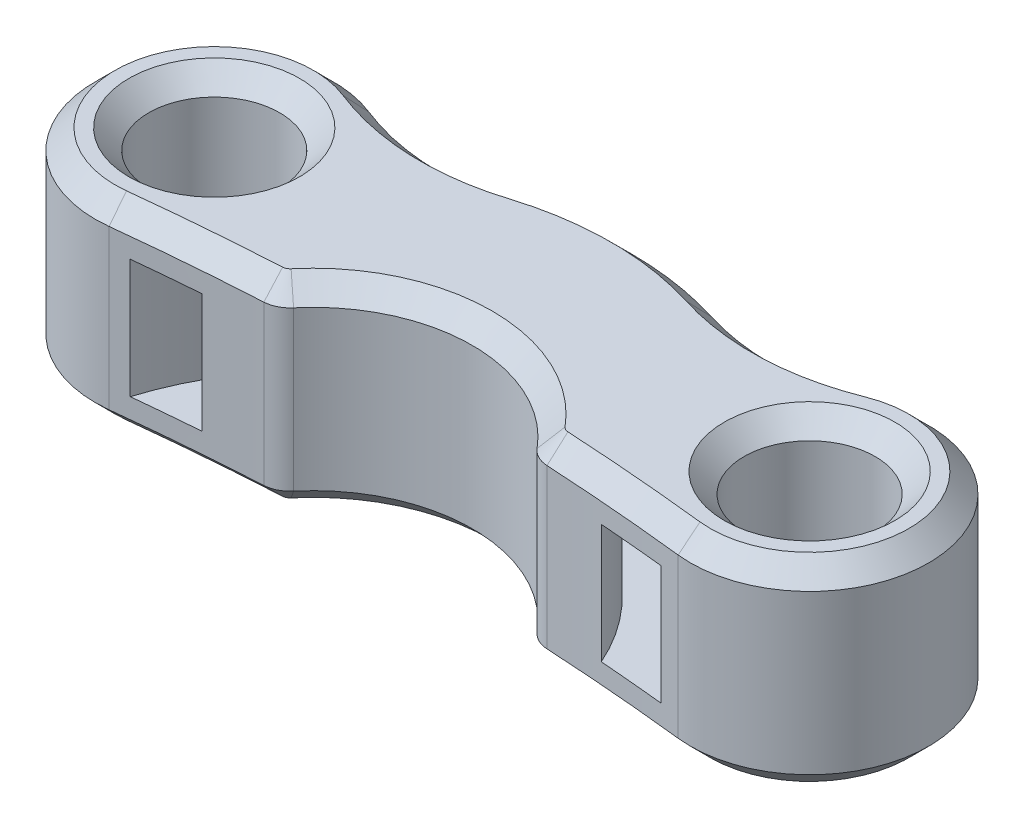
SolidWorks part; units mm, degrees
ref_plane "Front Plane" through (0, 0, 0) normal (0, 0, 1) x (1, 0, 0)
ref_plane "Top Plane" through (0, 0, 0) normal (0, 1, 0) x (1, 0, 0)
ref_plane "Right Plane" through (0, 0, 0) normal (1, 0, 0) x (0, 0, -1)
sketch "Sketch1" plane through (0, 0, 0) normal (0, 1, 0) x (1, 0, 0)
  line L0 (-7.5, 0) -> (7.5, 0) construction
  line L1 (0, 0) -> (0, 3) construction
  circle A0 centre (-7.5, 0) radius 1.65
  circle A1 centre (7.5, 0) radius 1.65
  circle A2 centre (0, -5) radius 4
  circle A3 centre (-7.5, 0) radius 3
  circle A4 centre (7.5, 0) radius 3
  circle A5 centre (0, -5) radius 8
  arc A6 (-6.3915, 2.7877) -> (-2.3855, 2.6361) centre (-4.1746, 8.3631) ccw
  arc A7 (6.3915, 2.7877) -> (2.3855, 2.6361) centre (4.1746, 8.3631) cw
  arc A9 (-7.1691, -2.9817) -> (7.1691, -2.9817) centre (0, -67.5851) cw
  dimension "D1" = 3.3
  dimension "D3" = 8
  dimension "D2" = 4
  dimension "D5" = 6
  dimension "D7" = 6
  dimension "D8" = 65
  dimension "D4" = 15
  dimension "D6" = 5
extrude "Boss-Extrude1" add sketch "Sketch1" along normal blind 5 contours A5 A3 A0 | A3 A5 A0 | A6 A3 A5 | A4 A7 A5 | A3 A9 A2 A4 A5 | A4 A5 A1 | A5 A4 A1
sketch "Sketch2" plane through (0, 0, 0) normal (1, 0, 0) x (0, 0, -1)
  line L0 (-1, 5) -> (-2.6664, 5) construction
  line L1 (-2.6664, 5) -> (-2.6664, 0) construction
  line L2 (-1, 5) -> (-2.6664, 5) construction
  line L3 (-2.6664, 5) -> (-2.6664, 0) construction
  line L4 (-5, 0) -> (-5, 5) construction
  line L5 (0.5, 1) -> (2, 1)
  line L6 (0.5, 1) -> (0.5, 4)
  line L7 (0.5, 4) -> (2, 4)
  line L8 (2, 1) -> (2, 4)
  line L9 (0.5, 1) -> (2, 4) construction
  line L10 (0.5, 4) -> (2, 1) construction
  point P2 (1.25, 2.5)
  point P8 (-2.6664, 2.5)
  dimension "D1" = 1.5
  dimension "D2" = 1.5
  dimension "D3" = 3
revolve "Cut-Revolve1" cut sketch "Sketch2" angle 360 about L4
fillet "Fillet1" radius 0.7 2 edges at (3.2487, 2.5, 2.6664) (-3.2487, 2.5, 2.6664)
chamfer "Chamfer1" distance 0.5 angle 45 24 edges at (-7.5, 5, 1.65) (-7.5, 0, 1.65) (7.5, 5, 1.65) (7.5, 0, 1.65) (10.4731, 0, -0.4007) (10.4731, 5, -0.4007) (4.4015, 0, -2.3674) (4.4015, 5, -2.3674) (0, 0, -3) (0, 5, -3) (-4.4015, 0, -2.3674) (-4.4015, 5, -2.3674) (-10.4731, 0, -0.4007) (-10.4731, 5, -0.4007) (-5.3698, 0, 2.8073) (-5.3698, 5, 2.8073) (-3.2912, 5, 2.6099) (-3.2912, 0, 2.6099) (0, 0, 1) (0, 5, 1) (3.2912, 5, 2.6099) (3.2912, 0, 2.6099) (5.3698, 5, 2.8073) (5.3698, 0, 2.8073)
